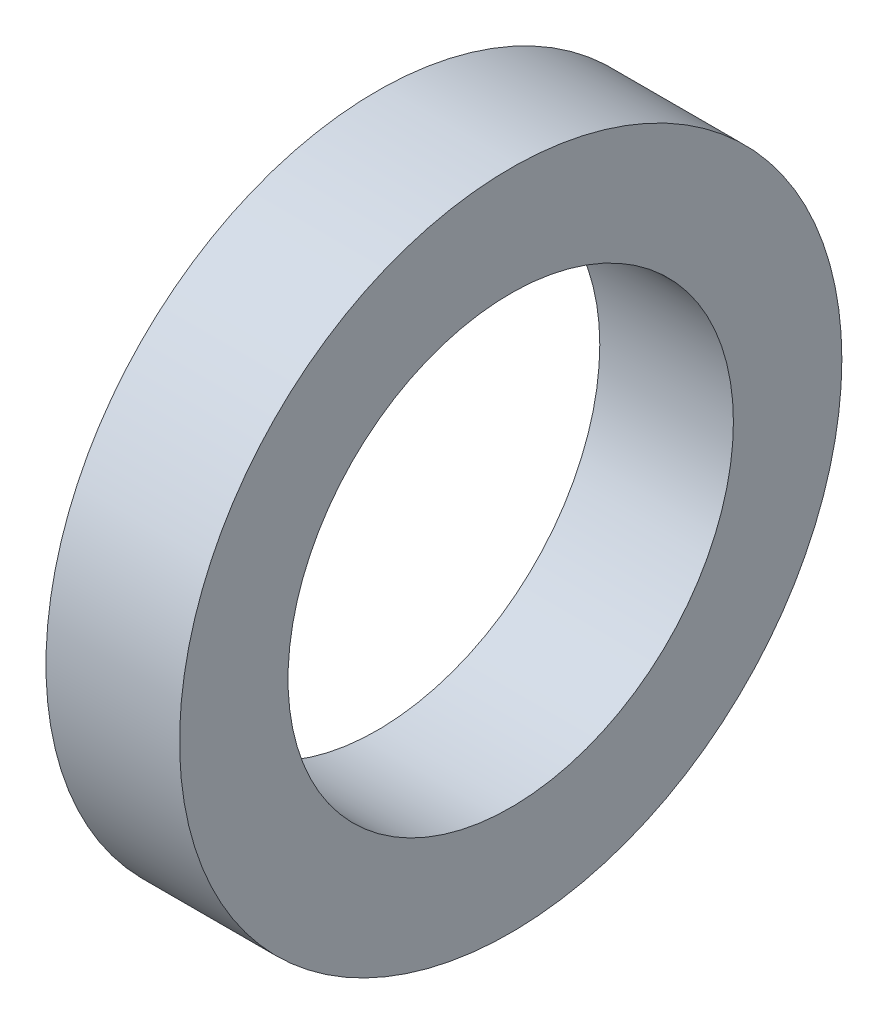
SolidWorks part; units mm, degrees
ref_plane "Front Plane" through (0, 0, 0) normal (0, 0, 1) x (1, 0, 0)
ref_plane "Top Plane" through (0, 0, 0) normal (0, 1, 0) x (1, 0, 0)
ref_plane "Right Plane" through (0, 0, 0) normal (1, 0, 0) x (0, 0, -1)
sketch "Sketch1" plane through (0, 0, 0) normal (1, 0, 0) x (0, 0, -1)
  circle A0 centre (0, 0) radius 31.75
  circle A1 centre (0, 0) radius 47.2122
  dimension "D1" = 63.5
  dimension "D2" = 94.4245
extrude "Boss-Extrude1" add sketch "Sketch1" along normal mid plane 19.05
